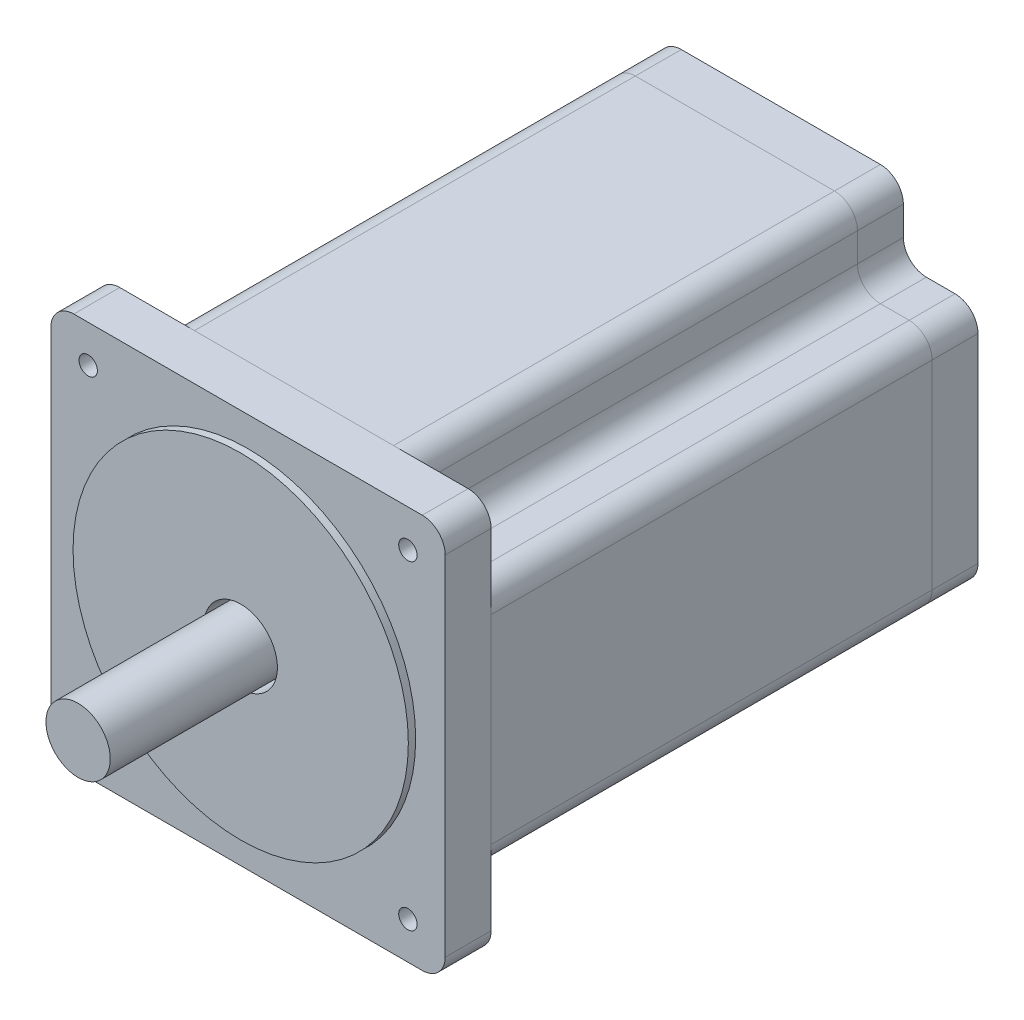
SolidWorks part; units mm, degrees
ref_plane "Płaszczyzna przednia" through (0, 0, 0) normal (0, 0, 1) x (1, 0, 0)
ref_plane "Płaszczyzna górna" through (0, 0, 0) normal (0, 1, 0) x (1, 0, 0)
ref_plane "Płaszczyzna prawa" through (0, 0, 0) normal (1, 0, 0) x (0, 0, -1)
sketch "Szkic1" plane through (0, 0, 0) normal (0, 0, 1) x (1, 0, 0)
  line L1 (42.925, -42.925) -> (-42.925, -42.925)
  line L2 (42.925, -42.925) -> (42.925, 42.925)
  line L3 (42.925, 42.925) -> (-42.925, 42.925)
  line L4 (-42.925, -42.925) -> (-42.925, 42.925)
  line L5 (42.925, -42.925) -> (-42.925, 42.925) construction
  line L6 (42.925, 42.925) -> (-42.925, -42.925) construction
  point P0 (0, 0)
  dimension "D1" = 85.85
  dimension "D2" = 85.85
extrude "Dodanie-wyciągnięcie2" add sketch "Szkic1" along normal blind 116 contours L3 L4 L1 L2
sketch "Szkic3" plane through (0, 0, 116) normal (0, 0, 1) x (1, 0, 0)
  circle A0 centre (0, 0) radius 36.5
extrude "Dodanie-wyciągnięcie3" add sketch "Szkic3" along normal blind 1.6
sketch "Szkic5" plane through (0, 0, 0) normal (0, 0, -1) x (-1, 0, 0)
  line L1 (-42.925, 42.925) -> (-26.675, 42.925)
  line L2 (-42.925, 42.925) -> (-42.925, 26.675)
  line L3 (-42.925, 26.675) -> (-26.675, 26.675)
  line L4 (-26.675, 42.925) -> (-26.675, 26.675)
  dimension "D1" = 16.25
  dimension "D2" = 16.25
extrude "Wytnij-wyciągnięcie1" cut sketch "Szkic5" against normal blind 106
pattern_linear "Szyk liniowy1" count 2 spacing 69.6 along (-1, 0, 0) count 2 spacing 69.6 along (0, -1, 0) of "Wytnij-wyciągnięcie1"
sketch "Szkic6" plane through (0, 0, 116) normal (0, 0, 1) x (1, 0, 0)
  line L0 (42.925, 42.925) -> (-42.925, 42.925) construction
  line L1 (-42.925, -42.925) -> (-42.925, 42.925) construction
  circle A0 centre (-34.8, 34.8) radius 2
  dimension "D1" = 8.125
  dimension "D2" = 8.125
extrude "Wytnij-wyciągnięcie2" cut sketch "Szkic6" against normal blind 10
pattern_linear "Szyk liniowy2" count 2 spacing 69.6 along (1, 0, 0) count 2 spacing 69.6 along (0, -1, 0) of "Wytnij-wyciągnięcie2"
sketch "Szkic7" plane through (0, 0, 117.6) normal (0, 0, 1) x (1, 0, 0)
  circle A0 centre (0, 0) radius 7
  dimension "D1" = 14
extrude "Dodanie-wyciągnięcie4" add sketch "Szkic7" along normal blind 35.4
sketch "Szkic8" plane through (0, 0, 117.6) normal (0, 0, 1) x (1, 0, 0)
  circle A0 centre (0, 0) radius 7
  circle A1 centre (0, 0) radius 8
  dimension "D1" = 16
  dimension "D2" = 14
extrude "Wytnij-wyciągnięcie5" cut sketch "Szkic8" against normal blind 10
sketch "Szkic10" plane through (0, 0, 153) normal (0, 0, 1) x (1, 0, 0)
  line L1 (-4.0051, 7) -> (3.6084, 7)
  line L2 (-4.0051, 7) -> (-4.0051, 5.35)
  line L3 (-4.0051, 5.35) -> (3.6084, 5.35)
  line L4 (3.6084, 7) -> (3.6084, 5.35)
  circle A0 centre (0, 0) radius 7 construction
extrude "Wytnij-wyciągnięcie6" [suppressed] cut sketch "Szkic10" against normal blind 25
fillet "Zaokrąglenie1" radius 5 4 edges at (-42.925, -42.925, 111) (42.925, -42.925, 111) (-42.925, 42.925, 111) (42.925, 42.925, 111)
fillet "Zaokrąglenie2" radius 5 8 edges at (42.925, -26.675, 53) (-42.925, 26.675, 53) (26.675, -42.925, 53) (-26.675, -42.925, 53) (-42.925, -26.675, 53) (-26.675, 42.925, 53) (26.675, 42.925, 53) (42.925, 26.675, 53)
fillet "Zaokrąglenie3" radius 5 4 edges at (26.675, -26.675, 53) (26.675, 26.675, 53) (-26.675, 26.675, 53) (-26.675, -26.675, 53)
sketch "Szkic14" plane through (-42.925, 0, 0) normal (-1, 0, 0) x (0, 0, 1)
  line L0 (106, 42.925) -> (106, -42.925)
split line "Linia podziałowa1"
sketch "Szkic20" plane through (0, 42.925, 0) normal (0, 1, 0) x (1, 0, 0)
  line L0 (-53.5046, -10) -> (51.8443, -10)
  line L1 (21.675, 0) -> (-21.675, 0) construction
  dimension "D1" = 10
split line "Linia podziałowa2"
